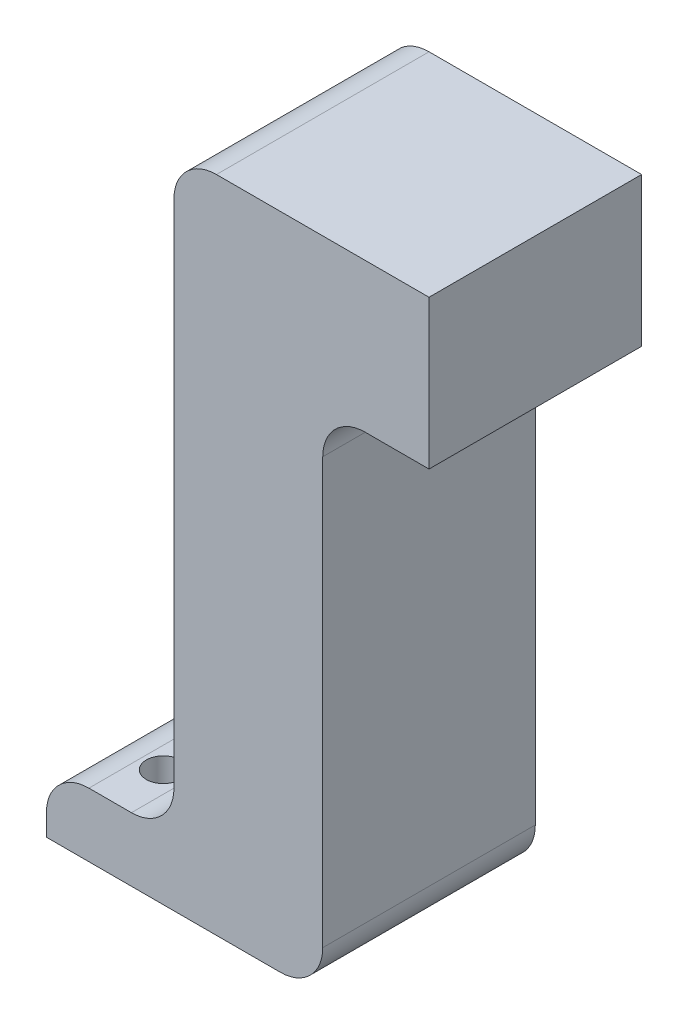
SolidWorks part; units mm, degrees
ref_plane "Front Plane" through (0, 0, 0) normal (0, 0, 1) x (1, 0, 0)
ref_plane "Top Plane" through (0, 0, 0) normal (0, 1, 0) x (1, 0, 0)
ref_plane "Right Plane" through (0, 0, 0) normal (1, 0, 0) x (0, 0, -1)
sketch "Sketch1" plane through (0, 0, 0) normal (0, 0, 1) x (1, 0, 0)
  line L0 (-1.4642, 0.25) -> (-1.4642, -5.75)
  line L5 (-1.4642, 0.25) -> (1.5358, 0.25)
  line L6 (-1.4642, 0.25) -> (-1.4642, 2)
  line L7 (-1.4642, 2) -> (1.5358, 2)
  line L8 (1.5358, 0.25) -> (1.5358, 2)
  line L9 (-1.4642, -5.75) -> (-2.9642, -5.75)
  line L10 (-1.4642, -5.75) -> (-1.4642, -5)
  line L11 (-1.4642, -5) -> (-2.9642, -5)
  line L12 (-2.9642, -5.75) -> (-2.9642, -5)
  line L13 (-1.4642, 0.25) -> (0.2858, 0.25)
  line L14 (-1.4642, -5.75) -> (0.2858, -5.75)
  line L15 (0.2858, 0.25) -> (0.2858, -5.75)
  dimension "D1" = 1.75
  dimension "D2" = 3
  dimension "D3" = 0
  dimension "D4" = 1.75
  dimension "D5" = 0.75
  dimension "D6" = 6
  dimension "D7" = 1.5
extrude "Boss-Extrude1" add sketch "Sketch1" along normal blind 1.875 and the other way blind 0.625 contours L5 L8 L7 L6 | L12 L9 L0 L11
fillet "Fillet1" radius 0.5 5 edges at (0.2858, 0.25, 0.625) (-1.4642, 2, 0.625) (-2.9642, -5, 0.625) (0.2858, -5.75, 0.625) (-1.4642, -5, 0.625)
hole_wizard "Ø0.4 (0.4) Diameter Hole1" positions "Sketch2" profile "Sketch3" hole size "Ø0.4" standard "DIN" end condition through all
sketch "Sketch2" plane through (0, -5, 0) normal (0, 1, 0) x (1, 0, 0)
  line L0 (-1.4642, 0) -> (-2.9642, 0) construction
  point P0 (-2.2142, 0)
  point P4 (-2.2142, -1.25)
  dimension "D1" = 1.25
sketch "Sketch3" plane through (-2.2142, -5, 0) normal (1, 0, 0) x (0, 0, 1)
  line L0 (0, 0) -> (0, 0.75)
  line L1 (0, 0.75) -> (0.2, 0.75)
  line L2 (0.2, 0.75) -> (0.2, 0)
  line L5 (0.2, 0) -> (0, 0)
  line L11 (0, -6.35) -> (0, 107.95) construction
  dimension "Thru Hole Dia." = 0.4
  dimension "Thru Hole Depth" = 0.75
